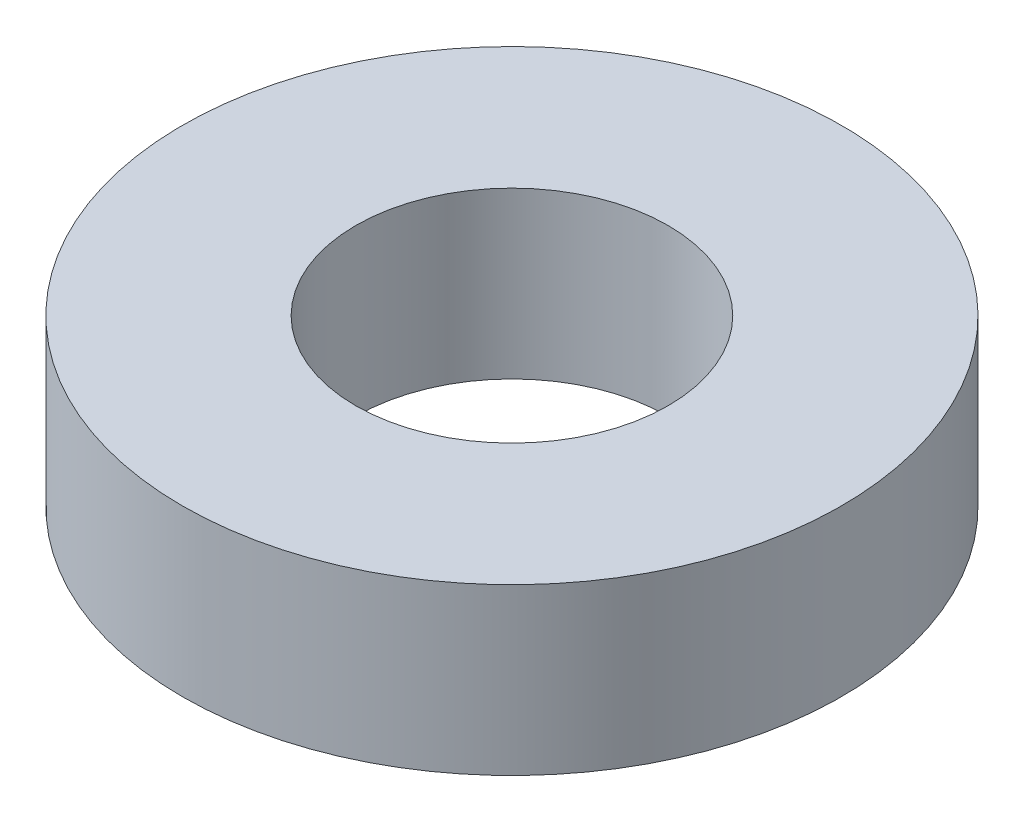
SolidWorks part; units mm, degrees
ref_plane "Front Plane" through (0, 0, 0) normal (0, 0, 1) x (1, 0, 0)
ref_plane "Top Plane" through (0, 0, 0) normal (0, 1, 0) x (1, 0, 0)
ref_plane "Right Plane" through (0, 0, 0) normal (1, 0, 0) x (0, 0, -1)
sketch "Sketch1" plane through (0, 0, 0) normal (0, 1, 0) x (1, 0, 0)
  circle A0 centre (4.2636, -12.6054) radius 3.1657
extrude "M3 nylon washer" add sketch "Sketch1" along normal blind 1.5875
hole_wizard "Ø3.0 (3) Diameter Hole1" positions "Sketch5" profile "Sketch4" hole size "Ø3.0" standard "Ansi Metric"
sketch "Sketch5" plane through (0, 1.5875, 0) normal (0, 1, 0) x (-1, 0, 0)
  circle A0 centre (-4.2636, 12.6054) radius 3.1657 construction
  point P0 (-4.2636, 12.6054)
sketch "Sketch4" plane through (4.2636, 1.5875, 12.6054) normal (1, 0, 0) x (0, 0, 1)
  line L0 (0, 0) -> (0, 26.3013)
  line L1 (0, 26.3013) -> (1.5, 25.4)
  line L2 (1.5, 25.4) -> (1.5, 0)
  line L5 (1.5, 0) -> (0, 0)
  line L10 (0, 26.3013) -> (-1.5, 25.4) construction
  line L11 (0, -6.35) -> (0, 107.95) construction
  dimension "Hole Dia." = 3
  dimension "Hole Depth" = 25.4
  dimension "Drill Angle" = 118
